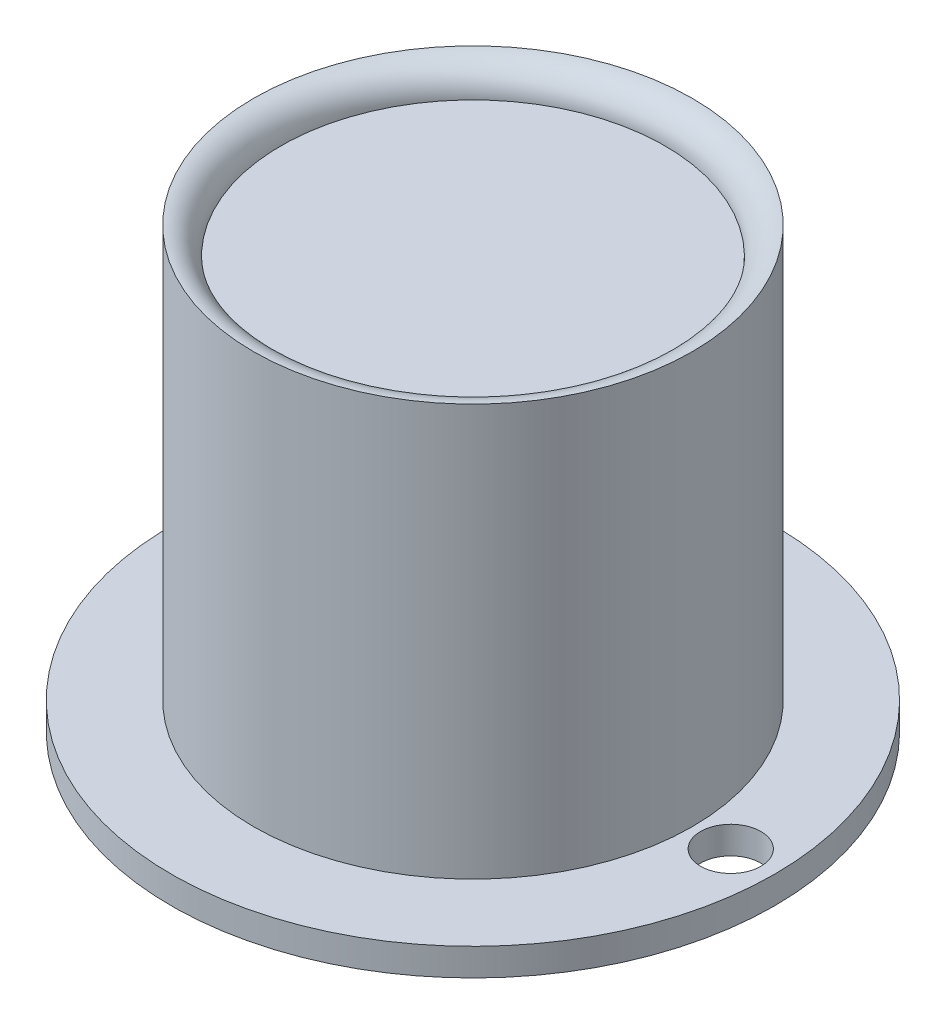
SolidWorks part; units mm, degrees
ref_plane "前视基准面" through (0, 0, 0) normal (0, 0, 1) x (1, 0, 0)
ref_plane "上视基准面" through (0, 0, 0) normal (0, 1, 0) x (1, 0, 0)
ref_plane "右视基准面" through (0, 0, 0) normal (1, 0, 0) x (0, 0, -1)
sketch "草图1" plane through (0, 0, 0) normal (0, 0, 1) x (1, 0, 0)
  line L0 (0, 16.5276) -> (0, 0) construction
  line L1 (0, 0) -> (-15.06, 0) construction
  line L2 (0, 14) -> (-7, 14)
  line L3 (-8, 15) -> (-8, 0)
  line L4 (-8, 0) -> (0, 0)
  line L5 (0, 0) -> (0, 14)
  arc A1 (-7, 14) -> (-8, 15) centre (-8, 14) ccw
  dimension "D1" = 8
  dimension "D2" = 7
  dimension "D3" = 15
revolve "旋转1" add sketch "草图1" angle 360 about L5
sketch "草图2" plane through (0, 0, 0) normal (0, -1, 0) x (1, 0, 0)
  circle A0 centre (0, 0) radius 7
  dimension "D1" = 14
extrude "切除-拉伸1" cut sketch "草图2" against normal blind 10
sketch "草图3" plane through (0, 0, 0) normal (0, -1, 0) x (1, 0, 0)
  circle A0 centre (0, 0) radius 11
  circle A1 centre (0, 0) radius 8 construction
  circle A2 centre (0, 0) radius 7
  circle A3 centre (0, 0) radius 7 construction
  dimension "D1" = 3
extrude "凸台-拉伸1" add sketch "草图3" along normal blind 1
sketch "草图4" plane through (0, -1, 0) normal (0, -1, 0) x (1, 0, 0)
  line L0 (0, 0) -> (0, 11) construction
  line L1 (8.3, 0) -> (10.5, 0) construction
  circle A0 centre (9.4, 0) radius 1.1
  circle A3 centre (0, 0) radius 9.4 construction
  circle A4 centre (0, 0) radius 7 construction
  circle A5 centre (0, 0) radius 11 construction
  circle A6 centre (-9.4, 0) radius 1.1
  dimension "D1" = 2.4
  dimension "D2" = 2.2
extrude "切除-拉伸2" cut sketch "草图4" against normal up to surface (1 mm away) up to face at (8, 0, 0)
sketch "草图5" plane through (0, -1, 0) normal (0, -1, 0) x (1, 0, 0)
  line L0 (10.5, 0) -> (8.3, 0) construction
  circle A0 centre (9.4, 0) radius 1.1 construction
